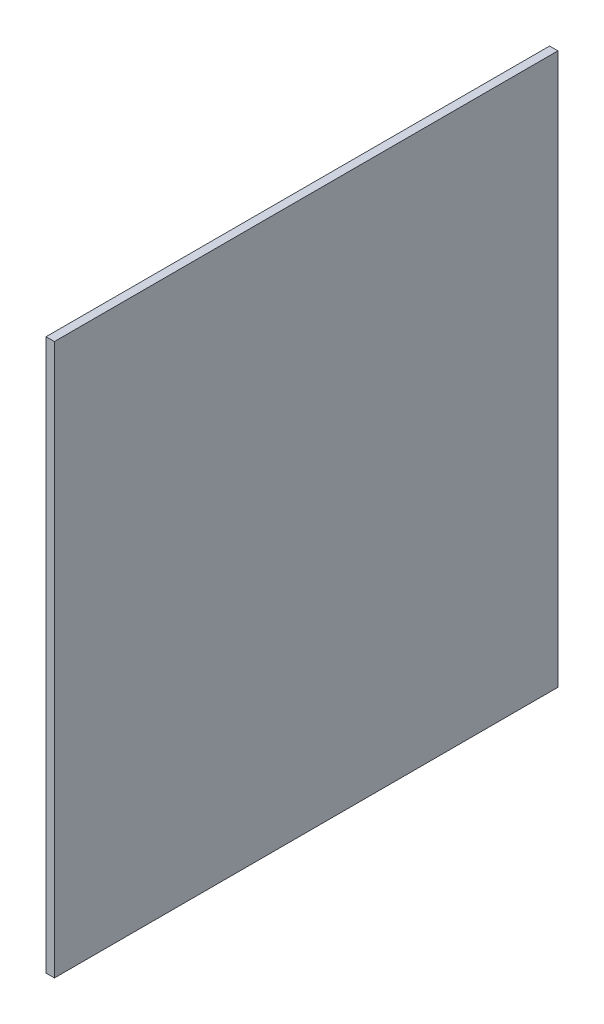
SolidWorks part; units mm, degrees
ref_plane "Front Plane" through (0, 0, 0) normal (0, 0, 1) x (1, 0, 0)
ref_plane "Top Plane" through (0, 0, 0) normal (0, 1, 0) x (1, 0, 0)
ref_plane "Right Plane" through (0, 0, 0) normal (1, 0, 0) x (0, 0, -1)
sketch "Sketch1" plane through (0, -457.2, 0) normal (0, 1, 0) x (1, 0, 0)
  line L1 (2235.2, 370.4871) -> (2247.9, 370.4871)
  line L2 (2235.2, 370.4871) -> (2235.2, -395.2054)
  line L3 (2235.2, -395.2054) -> (2247.9, -395.2054)
  line L4 (2247.9, 370.4871) -> (2247.9, -395.2054)
  line L5 (548.8742, 251.2508) -> (-0.8891, 212.6688) construction
  dimension "D1" = 12.7
  dimension "D2" = 2235.2
extrude "Boss-Extrude1" add sketch "Sketch1" along normal blind 838.2
